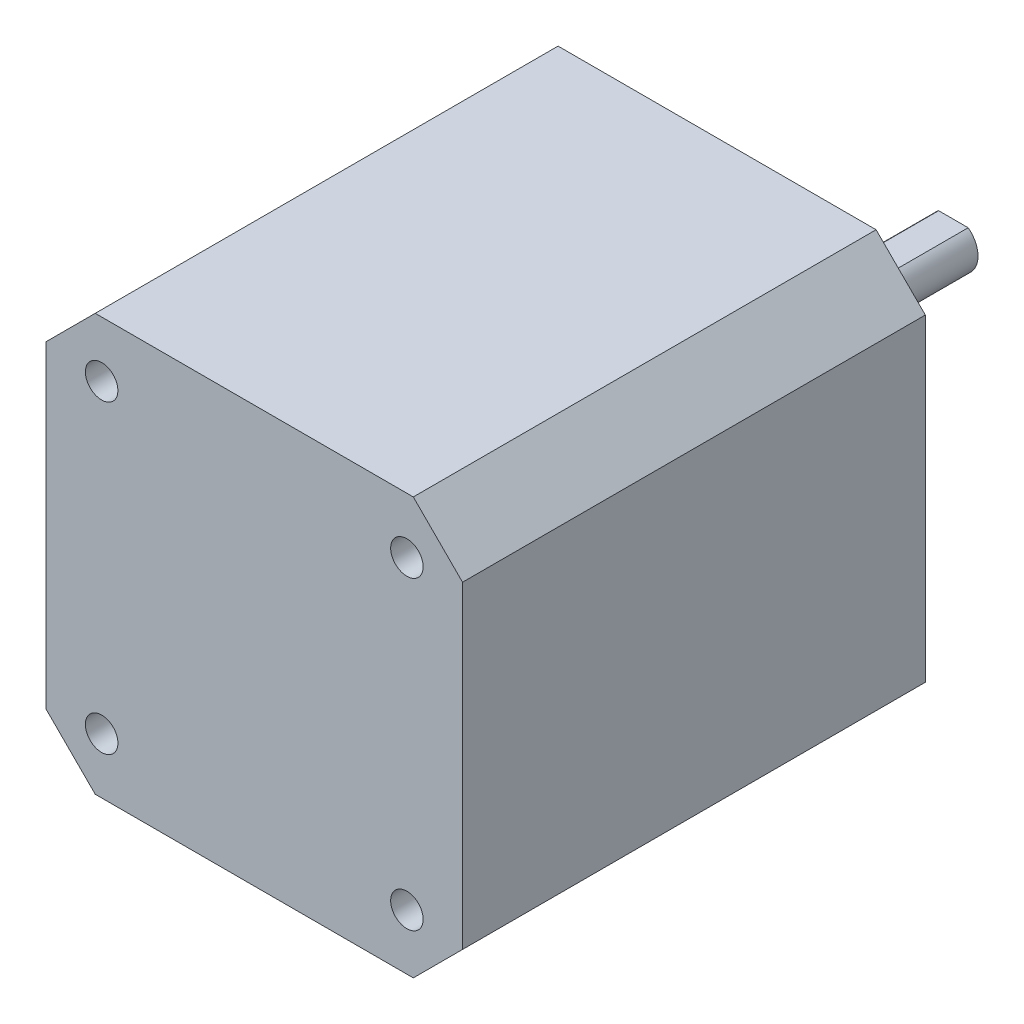
SolidWorks part; units mm, degrees
ref_plane "前视基准面" through (0, 0, 0) normal (0, 0, 1) x (1, 0, 0)
ref_plane "上视基准面" through (0, 0, 0) normal (0, 1, 0) x (1, 0, 0)
ref_plane "右视基准面" through (0, 0, 0) normal (1, 0, 0) x (0, 0, -1)
sketch "草图1" plane through (0, 0, 0) normal (0, 0, 1) x (1, 0, 0)
  line L0 (-21.15, 16.15) -> (-16.15, 21.15)
  line L1 (-16.15, 21.15) -> (16.15, 21.15)
  line L2 (-21.15, 16.15) -> (-21.15, -16.15)
  line L3 (-16.15, -21.15) -> (16.15, -21.15)
  line L4 (21.15, 16.15) -> (21.15, -16.15)
  line L5 (-21.15, 21.15) -> (21.15, -21.15) construction
  line L6 (-21.15, -21.15) -> (21.15, 21.15) construction
  line L7 (16.15, 21.15) -> (21.15, 16.15)
  line L8 (16.15, -21.15) -> (21.15, -16.15)
  line L9 (-21.15, -16.15) -> (-16.15, -21.15)
  line L10 (0, 0) -> (0, 11) construction
  line L11 (11, 0) -> (0, 0) construction
  circle A1 centre (15.5, 15.5) radius 1.65
  circle A2 centre (-15.5, 15.5) radius 1.65
  circle A3 centre (15.5, -15.5) radius 1.65
  circle A4 centre (-15.5, -15.5) radius 1.65
  point P0 (0, 0)
  dimension "D4" = 3.3
  dimension "D1" = 42.3
  dimension "D2" = 42.3
  dimension "D5" = 31
extrude "凸台-拉伸1" add sketch "草图1" along normal blind 47
sketch "草图3" plane through (0, 0, 0) normal (0, 0, -1) x (-1, 0, 0)
  circle A0 centre (0, 0) radius 11
  dimension "D1" = 22
extrude "凸台-拉伸2" add sketch "草图3" along normal blind 2
sketch "草图4" plane through (0, 0, -2) normal (0, 0, -1) x (-1, 0, 0)
  line L0 (-1.5, 2) -> (1.5, 2)
  arc A0 (-1.5, 2) -> (1.5, 2) centre (0, 0) ccw
  dimension "D1" = 5
  dimension "D2" = 2
extrude "凸台-拉伸3" add sketch "草图4" along normal blind 22
